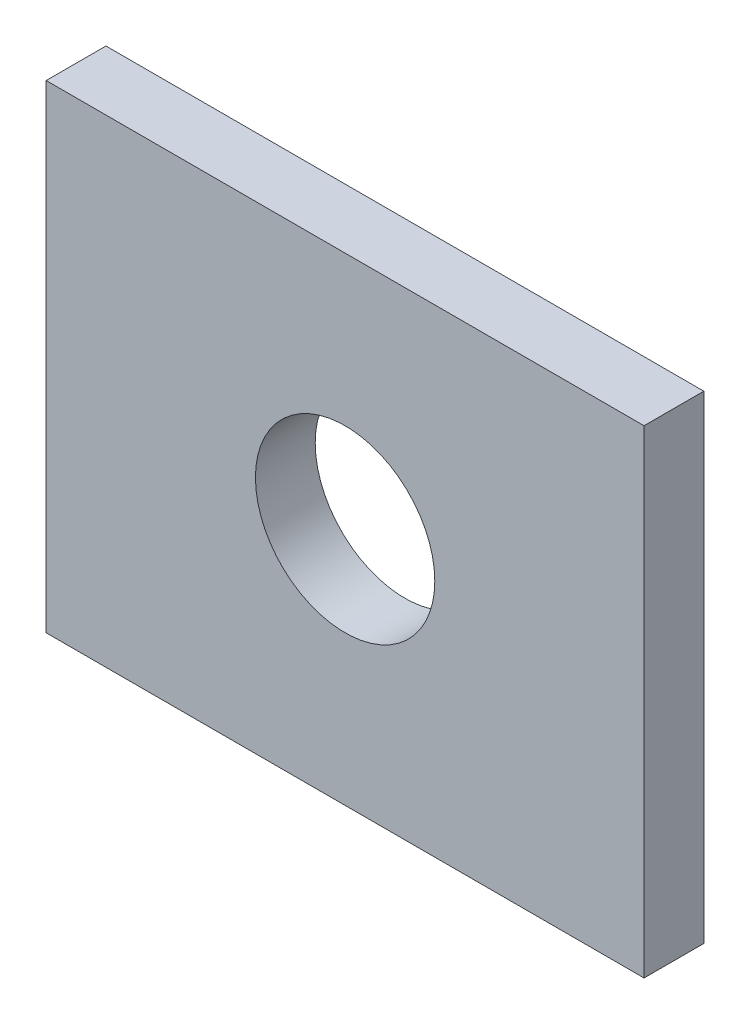
SolidWorks part; units mm, degrees
ref_plane "Front Plane" through (0, 0, 0) normal (0, 0, 1) x (1, 0, 0)
ref_plane "Top Plane" through (0, 0, 0) normal (0, 1, 0) x (1, 0, 0)
ref_plane "Right Plane" through (0, 0, 0) normal (1, 0, 0) x (0, 0, -1)
sketch "Sketch1" plane through (0, 0, 0) normal (0, 0, 1) x (1, 0, 0)
  line L1 (5, -4) -> (-5, -4)
  line L2 (5, -4) -> (5, 4)
  line L3 (5, 4) -> (-5, 4)
  line L4 (-5, -4) -> (-5, 4)
  line L5 (5, -4) -> (-5, 4) construction
  line L6 (5, 4) -> (-5, -4) construction
  circle A0 centre (0, 0) radius 1.5
  point P0 (0, 0)
  dimension "D3" = 3
  dimension "D1" = 10
  dimension "D2" = 8
extrude "Boss-Extrude1" add sketch "Sketch1" along normal mid plane 1
